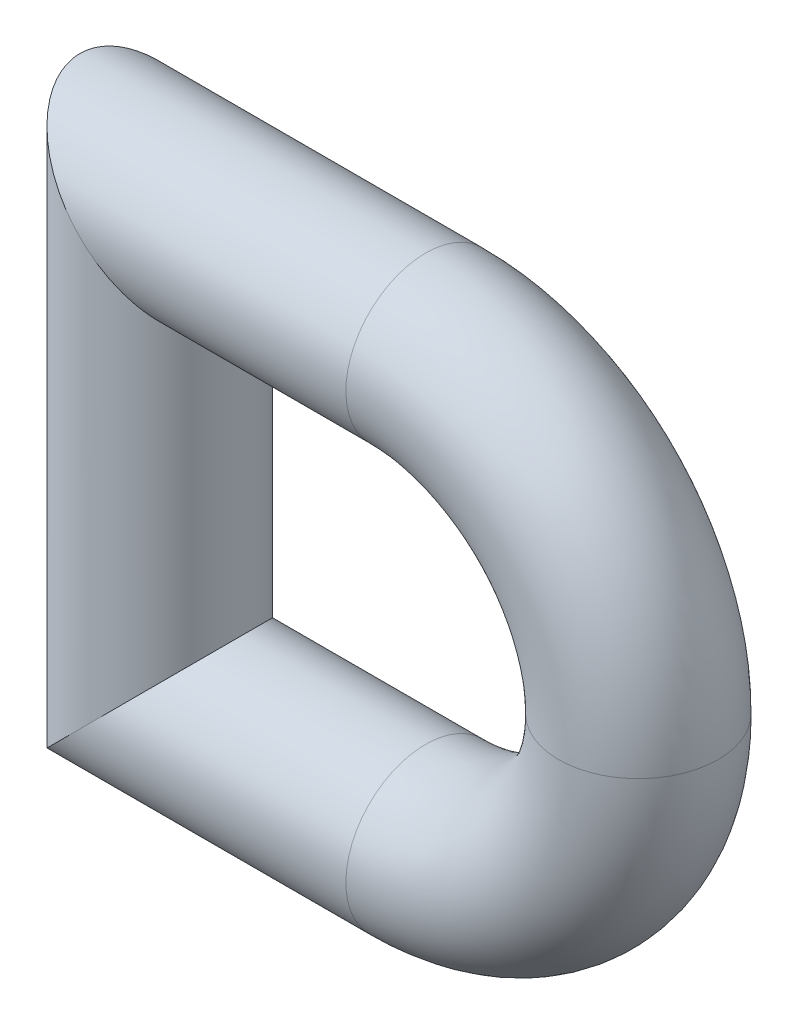
SolidWorks part; units mm, degrees
ref_plane "Front Plane" through (0, 0, 0) normal (0, 0, 1) x (1, 0, 0)
ref_plane "Top Plane" through (0, 0, 0) normal (0, 1, 0) x (1, 0, 0)
ref_plane "Right Plane" through (0, 0, 0) normal (1, 0, 0) x (0, 0, -1)
sketch "Sketch1" plane through (0, 0, 0) normal (0, 0, 1) x (1, 0, 0)
  line L0 (0, -8) -> (0, 8)
  line L1 (0, 8) -> (10, 8)
  line L2 (0, -8) -> (10, -8)
  line L3 (0, 0) -> (10, 0) construction
  line L4 (10, 0) -> (14, 0) construction
  line L5 (14, 0) -> (18, 0) construction
  arc A0 (10, 8) -> (10, -8) centre (10, 0) cw
  point P4 (0, 0)
  dimension "D2" = 10
  dimension "D1" = 16
  dimension "D4" = 14
sketch "Sketch2" plane through (0, 0, 0) normal (0, 1, 0) x (1, 0, 0)
  line L0 (14, 0) -> (18, 0) construction
  circle A0 centre (18, 0) radius 3
  dimension "D1" = 6
sweep "Sweep1" add profiles "Sketch2" path "Sketch1"
